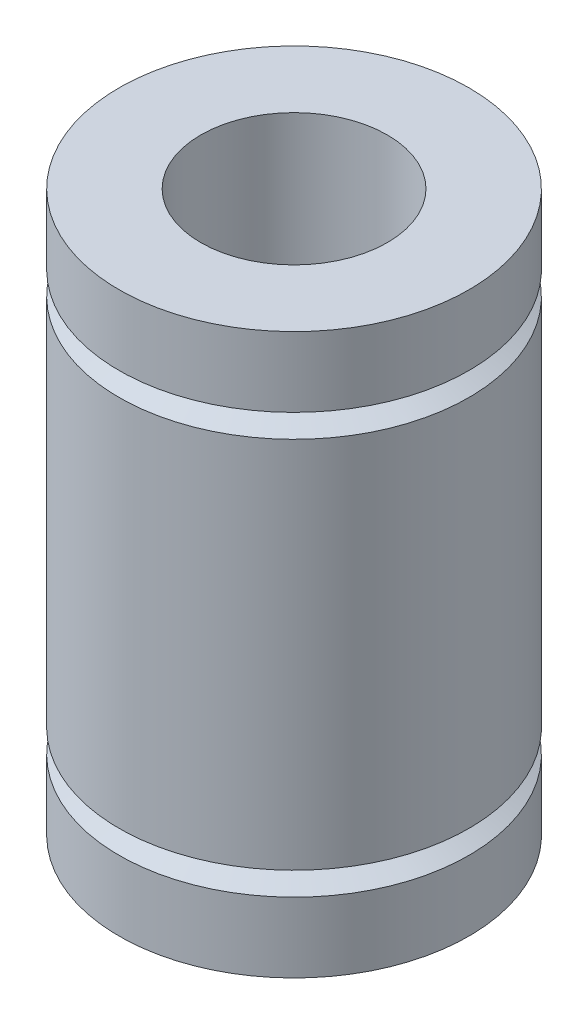
SolidWorks part; units mm, degrees
ref_plane "前视基准面" through (0, 0, 0) normal (0, 0, 1) x (1, 0, 0)
ref_plane "上视基准面" through (0, 0, 0) normal (0, 1, 0) x (1, 0, 0)
ref_plane "右视基准面" through (0, 0, 0) normal (1, 0, 0) x (0, 0, -1)
sketch "草图1" plane through (0, 0, 0) normal (0, 0, 1) x (1, 0, 0)
  line L0 (-52.5, 24) -> (-56, 24)
  line L1 (-56, 24) -> (-56, 0)
  line L2 (-56, 0) -> (-52.5, 0)
  line L3 (-52.5, 0) -> (-52.5, 3)
  line L4 (-52.5, 3) -> (-53.5, 3.5)
  line L5 (-53.5, 3.5) -> (-52.5, 4)
  line L6 (-52.5, 4) -> (-52.5, 20)
  line L7 (-52.5, 20) -> (-53.5, 20.5)
  line L8 (-53.5, 20.5) -> (-52.5, 21)
  line L9 (-52.5, 21) -> (-52.5, 24)
  line L10 (-60, 24) -> (-60, 0) construction
revolve "旋转1" add sketch "草图1" angle 360 about L10
